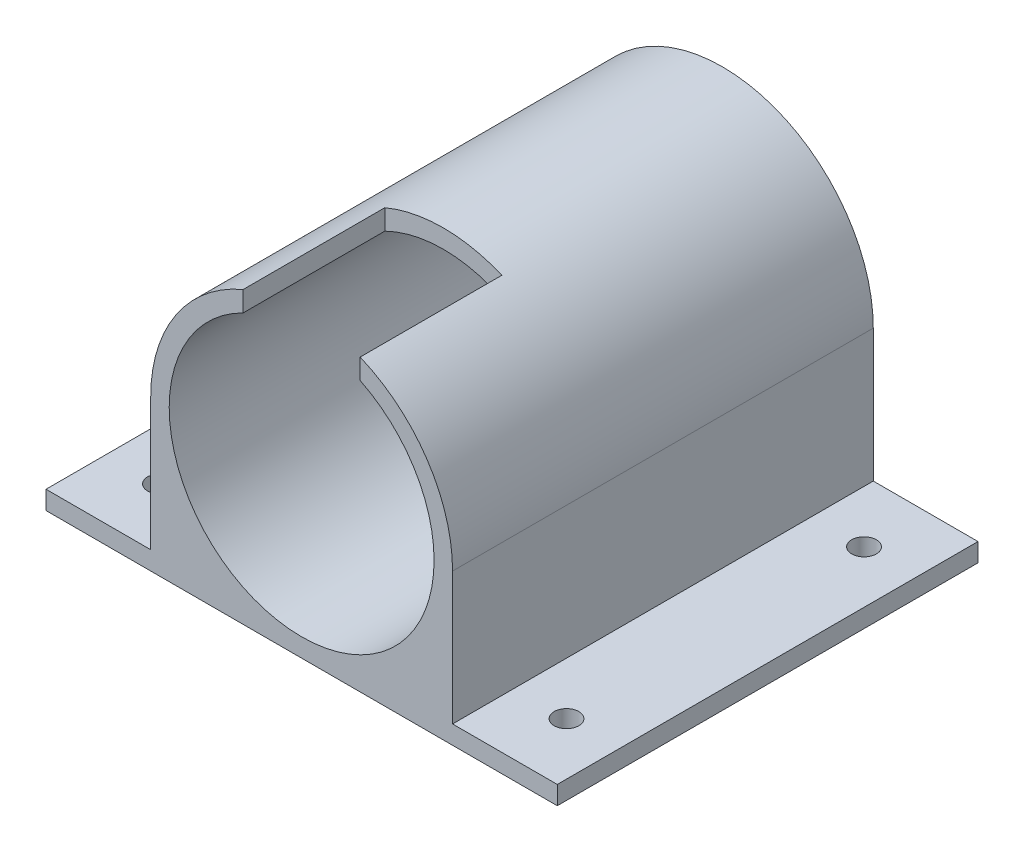
SolidWorks part; units mm, degrees
ref_plane "Plan de face" through (0, 0, 0) normal (0, 0, 1) x (1, 0, 0)
ref_plane "Plan de dessus" through (0, 0, 0) normal (0, 1, 0) x (1, 0, 0)
ref_plane "Plan de droite" through (0, 0, 0) normal (1, 0, 0) x (0, 0, -1)
sketch "Esquisse1" plane through (0, 0, 0) normal (0, 0, 1) x (1, 0, 0)
  line L1 (-24.5, -24.5) -> (24.5, -24.5)
  line L2 (-24.5, -24.5) -> (-24.5, 0)
  line L4 (24.5, -24.5) -> (24.5, 0)
  line L5 (-24.5, -24.5) -> (17.3241, 17.3241) construction
  line L6 (-17.3241, 17.3241) -> (24.5, -24.5) construction
  circle A0 centre (0, 0) radius 24.5
  circle A1 centre (0, 0) radius 21.5
  dimension "D1" = 49
  dimension "D5" = 43
  dimension "D2" = 24.5
  dimension "D3" = 49
  dimension "D4" = 24.5
extrude "Boss.-Extru.1" add sketch "Esquisse1" along normal blind 65.3 contours A0 A1 | A0 L2 L1 | A0 L1 L4
sketch "Esquisse2" plane through (0, 0, 0) normal (0, 0, -1) x (-1, 0, 0)
  line L2 (-24.5, 0) -> (-24.5, -24.5)
  line L3 (-24.5, -24.5) -> (24.5, -24.5)
  line L4 (24.5, 0) -> (24.5, -24.5)
  line L5 (-17.3241, 17.3241) -> (24.5, -24.5) construction
  line L6 (-24.5, -24.5) -> (17.3241, 17.3241) construction
  circle A0 centre (0, 0) radius 24.5
  circle A1 centre (0, 0) radius 14.5
  circle M1 centre (0, 0) radius 21.5
  arc M2 (24.5, 0) -> (-24.5, 0) centre (0, 0) ccw
  line M3 (-24.5, 0) -> (-24.5, -24.5)
  line M4 (-24.5, -24.5) -> (24.5, -24.5)
  line M5 (24.5, -24.5) -> (24.5, 0)
  dimension "D1" = 29
extrude "Boss.-Extru.2" add sketch "Esquisse2" along normal blind 3 contours A1 M1 | A0 M2 M1 | A0 M3 M4 | A0 L3 M5
sketch "Esquisse3" plane through (0, 0, -3) normal (0, 0, -1) x (-1, 0, 0)
  line L0 (-17.5, 0) -> (17.5, 0) construction
  line L1 (0, 17.5) -> (0, -17.5) construction
  circle A0 centre (-17.5, 0) radius 1.65
  circle A1 centre (17.5, 0) radius 1.65
  circle A2 centre (0, 17.5) radius 1.65
  circle A3 centre (0, -17.5) radius 1.65
  point P3 (0, 0)
  point P8 (0, 0)
  dimension "D2" = 3.3
  dimension "D3" = 3.3
  dimension "D5" = 3.3
  dimension "D6" = 3.3
  dimension "D1" = 35
  dimension "D4" = 35
extrude "Enlèv. mat.-Extru.1" cut sketch "Esquisse3" against normal blind 3
sketch "Esquisse4" plane through (0, 0, 65.3) normal (0, 0, 1) x (1, 0, 0)
  line L0 (-9.5, 19.2873) -> (9.5, 19.2873) construction
  line L1 (-9.5, 19.2873) -> (-9.5, 25.0257) construction
  line L2 (-9.5, 25.0257) -> (9.5, 25.0257) construction
  line L3 (9.5, 25.0257) -> (9.5, 19.2873) construction
  line L4 (-9.5, 25.0257) -> (9.5, 25.0257)
  line L5 (9.5, 25.0257) -> (9.5, 19.2873)
  line L6 (9.5, 19.2873) -> (-9.5, 19.2873)
  line L7 (-9.5, 19.2873) -> (-9.5, 25.0257)
  circle A0 centre (0, 0) radius 21.5 construction
  dimension "D1" = 19
extrude "Enlèv. mat.-Extru.2" cut sketch "Esquisse4" against normal blind 23
sketch "Esquisse5" plane through (-24.5, 0, 0) normal (-1, 0, 0) x (0, 0, 1)
  line L0 (-3, -24.5) -> (-3, -21.5)
  line L1 (-3, -24.5) -> (-3, 0) construction
  line L2 (-3, -21.5) -> (65.3, -21.5)
  line L3 (65.3, -24.5) -> (65.3, 0) construction
  line L4 (65.3, -21.5) -> (65.3, -24.5)
  line L5 (65.3, -24.5) -> (-3, -24.5)
  dimension "D1" = 3
extrude "Boss.-Extru.3" add sketch "Esquisse5" along normal blind 17
sketch "Esquisse6" plane through (24.5, 0, 0) normal (1, 0, 0) x (0, 0, -1)
  line L0 (-65.3, -24.5) -> (-65.3, -21.5)
  line L1 (-65.3, -21.5) -> (3, -21.5)
  line L2 (3, -21.5) -> (3, -24.5)
  line L3 (3, -24.5) -> (-65.3, -24.5)
extrude "Boss.-Extru.4" add sketch "Esquisse6" along normal blind 17
sketch "Esquisse7" plane through (0, -21.5, 0) normal (0, 1, 0) x (1, 0, 0)
  line L0 (-24.5, -7) -> (-41.5, -7) construction
  line L1 (-24.5, -65.3) -> (-24.5, 3) construction
  line L2 (-41.5, -65.3) -> (-41.5, 3) construction
  line L3 (-41.5, 3) -> (-24.5, 3) construction
  line L4 (-24.5, -55.3) -> (-41.5, -55.3) construction
  line L5 (-41.5, -65.3) -> (-24.5, -65.3) construction
  circle A0 centre (-33, -7) radius 2
  circle A1 centre (-33, -55.3) radius 2
  dimension "D3" = 4
  dimension "D4" = 4
  dimension "D1" = 10
  dimension "D2" = 10
sketch "Esquisse9" plane through (0, -21.5, 0) normal (0, 1, 0) x (1, 0, 0)
  line L0 (24.5, -7) -> (41.5, -7) construction
  line L1 (24.5, 3) -> (24.5, -65.3) construction
  line L2 (41.5, 3) -> (41.5, -65.3) construction
  line L3 (24.5, -55.3) -> (41.5, -55.3) construction
  line L4 (41.5, 3) -> (24.5, 3) construction
  line L5 (41.5, -65.3) -> (24.5, -65.3) construction
  circle A0 centre (33, -7) radius 2
  circle A1 centre (33, -55.3) radius 2
  dimension "D3" = 4
  dimension "D4" = 4
  dimension "D1" = 10
  dimension "D2" = 10
extrude "Enlèv. mat.-Extru.3" cut sketch "Esquisse7" against normal blind 10
extrude "Enlèv. mat.-Extru.4" cut sketch "Esquisse9" against normal blind 10
